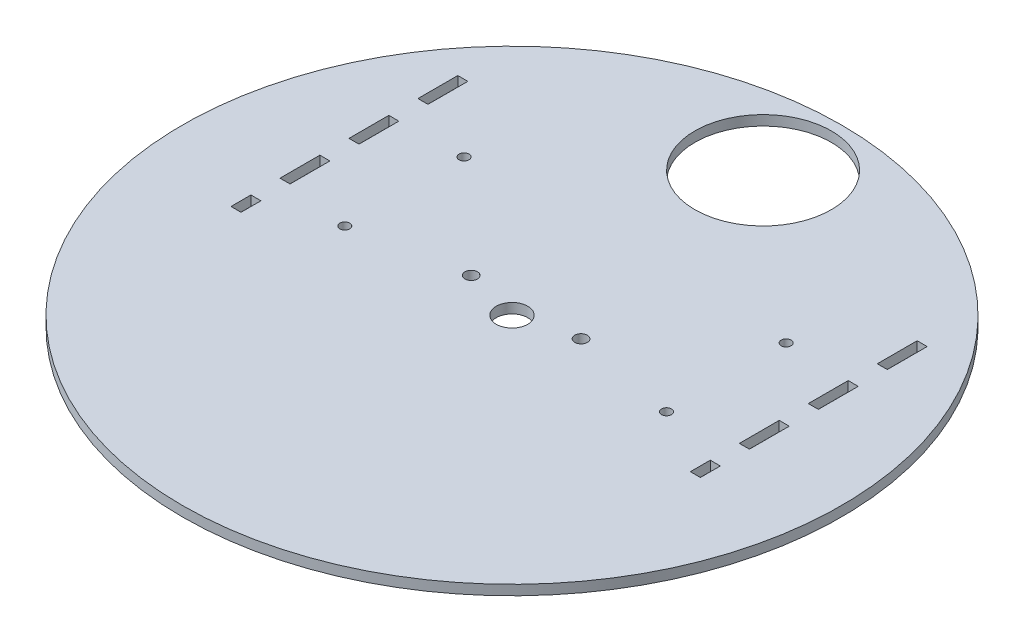
SolidWorks part; units mm, degrees
other "Markup1"
sketch "Sketch10" plane through (-105, 3.175, -105) normal (0, 1, 0) x (1, 0, 0)
ref_plane "Front Plane" through (0, 0, 0) normal (0, 0, 1) x (1, 0, 0)
ref_plane "Top Plane" through (0, 0, 0) normal (0, 1, 0) x (1, 0, 0)
ref_plane "Right Plane" through (0, 0, 0) normal (1, 0, 0) x (0, 0, -1)
sketch "Sketch2" plane through (0, 0, 0) normal (0, 1, 0) x (1, 0, 0)
  line L0 (0, 0) -> (0, 14.3166) construction
  circle A0 centre (0, 0) radius 105
  circle A1 centre (0, 80) radius 21.75
  circle A12 centre (0, 0) radius 5
  circle A17 centre (17.5, 4.5) radius 2
  circle A18 centre (-17.5, 4.5) radius 2
  point P17 (0, 0)
  point P26 (0, 0)
  dimension "D1" = 210
  dimension "D2" = 43.5
  dimension "D4" = 10
  dimension "D9" = 4
  dimension "D3" = 80
  dimension "D5" = 4.5
  dimension "D6" = 17.5
extrude "Boss-Extrude2" add sketch "Sketch2" along normal blind 3.175
sketch "Sketch6" plane through (0, 0, 0) normal (0, -1, 0) x (1, 0, 0)
  line L0 (-44.5097, 56.7801) -> (-44.5097, 44.0801)
  line L1 (-44.5097, 78.7511) -> (-41.3347, 78.7511)
  line L2 (-44.5097, 78.7511) -> (-44.5097, 66.0511)
  line L3 (-44.5097, 66.0511) -> (-41.3347, 66.0511)
  line L4 (-41.3347, 78.7511) -> (-41.3347, 66.0511)
  line L5 (-44.5097, 56.7801) -> (-41.3347, 56.7801)
  line L6 (-41.3347, 56.7801) -> (-41.3347, 44.0801)
  line L7 (-44.5097, 44.0801) -> (-41.3347, 44.0801)
  line L8 (-44.5097, 34.8091) -> (-44.5097, 22.1091)
  line L9 (-44.5097, 34.8091) -> (-41.3347, 34.8091)
  line L10 (-41.3347, 34.8091) -> (-41.3347, 22.1091)
  line L11 (-44.5097, 22.1091) -> (-41.3347, 22.1091)
  line L12 (-44.5097, 12.8381) -> (-44.5097, 6.4881)
  line L13 (-44.5097, 6.4881) -> (-41.3347, 6.4881)
  line L14 (-41.3347, 12.8381) -> (-41.3347, 6.4881)
  line L15 (-44.5097, 12.8381) -> (-41.3347, 12.8381)
  dimension "D1" = 12.7
  dimension "D2" = 3.175
  dimension "D5" = 9.271
  dimension "D6" = 9.271
  dimension "D4" = 6.35
  dimension "D3" = 3
sketch "Sketch8" plane through (0, 3.175, 0) normal (0, 1, 0) x (1, 0, 0)
  line L0 (0, 0) -> (0, 44.8041) construction
  line L1 (-74.777, 57.5071) -> (-71.577, 57.5071)
  line L2 (-74.777, 57.5071) -> (-74.777, 44.8041)
  line L3 (-74.777, 44.8041) -> (-71.577, 44.8041)
  line L4 (-71.577, 57.5071) -> (-71.577, 44.8041)
  line L5 (71.577, -8.4059) -> (71.577, -14.7589)
  line L6 (-74.777, 35.5361) -> (-71.577, 35.5361)
  line L7 (-74.777, 35.5361) -> (-74.777, 22.8331)
  line L8 (-74.777, 22.8331) -> (-71.577, 22.8331)
  line L9 (-71.577, 35.5361) -> (-71.577, 22.8331)
  line L10 (-74.777, 13.5651) -> (-71.577, 13.5651)
  line L11 (-74.777, 13.5651) -> (-74.777, 0.8621)
  line L12 (-74.777, 0.8621) -> (-71.577, 0.8621)
  line L13 (-71.577, 13.5651) -> (-71.577, 0.8621)
  line L14 (-74.777, -8.4059) -> (-71.577, -8.4059)
  line L15 (-74.777, -8.4059) -> (-74.777, -14.7589)
  line L16 (-74.777, -14.7589) -> (-71.577, -14.7589)
  line L17 (-71.577, -8.4059) -> (-71.577, -14.7589)
  line L18 (74.777, -14.7589) -> (71.577, -14.7589)
  line L19 (74.777, -8.4059) -> (74.777, -14.7589)
  line L20 (74.777, -8.4059) -> (71.577, -8.4059)
  line L21 (71.577, 13.5651) -> (71.577, 0.8621)
  line L22 (74.777, 0.8621) -> (71.577, 0.8621)
  line L23 (74.777, 13.5651) -> (74.777, 0.8621)
  line L24 (74.777, 13.5651) -> (71.577, 13.5651)
  line L25 (71.577, 35.5361) -> (71.577, 22.8331)
  line L26 (74.777, 22.8331) -> (71.577, 22.8331)
  line L27 (74.777, 35.5361) -> (74.777, 22.8331)
  line L28 (74.777, 35.5361) -> (71.577, 35.5361)
  line L29 (71.577, 57.5071) -> (71.577, 44.8041)
  line L30 (74.777, 44.8041) -> (71.577, 44.8041)
  line L31 (74.777, 57.5071) -> (74.777, 44.8041)
  line L32 (74.777, 57.5071) -> (71.577, 57.5071)
  point P52 (-71.577, -11.5824)
  point P53 (-71.577, 7.2136)
  point P54 (-71.577, 29.1846)
  point P55 (-71.577, 51.1556)
  dimension "D1" = 12.703
  dimension "D2" = 3.2
  dimension "D3" = 12.703
  dimension "D4" = 3.2
  dimension "D5" = 12.703
  dimension "D6" = 3.2
  dimension "D7" = 6.353
  dimension "D8" = 3.2
  dimension "D9" = 9.268
  dimension "D10" = 9.268
  dimension "D11" = 9.268
  dimension "D12" = 57.5071
  dimension "D13" = 71.577
  dimension "D14" = 71.577
  dimension "D15" = 71.577
  dimension "D21" = 18.796
  dimension "D22" = 21.971
  dimension "D23" = 21.971
  dimension "D27" = 71.577
extrude "Cut-Extrude1" cut sketch "Sketch8" against normal through all
sketch "Sketch9" plane through (0, 0, 0) normal (0, -1, 0) x (1, 0, 0)
  line L0 (0, 0) -> (0, -88.2305) construction
  circle A0 centre (51.2501, 2.0166) radius 1.5875
  circle A1 centre (-51.3151, -36.0326) radius 1.5875
  circle A2 centre (-51.2501, 2.0166) radius 1.5875
  circle A3 centre (51.3151, -36.0326) radius 1.5875
extrude "Cut-Extrude2" cut sketch "Sketch9" against normal through all
equation "\"D2@Sketch2\"=43.5"
